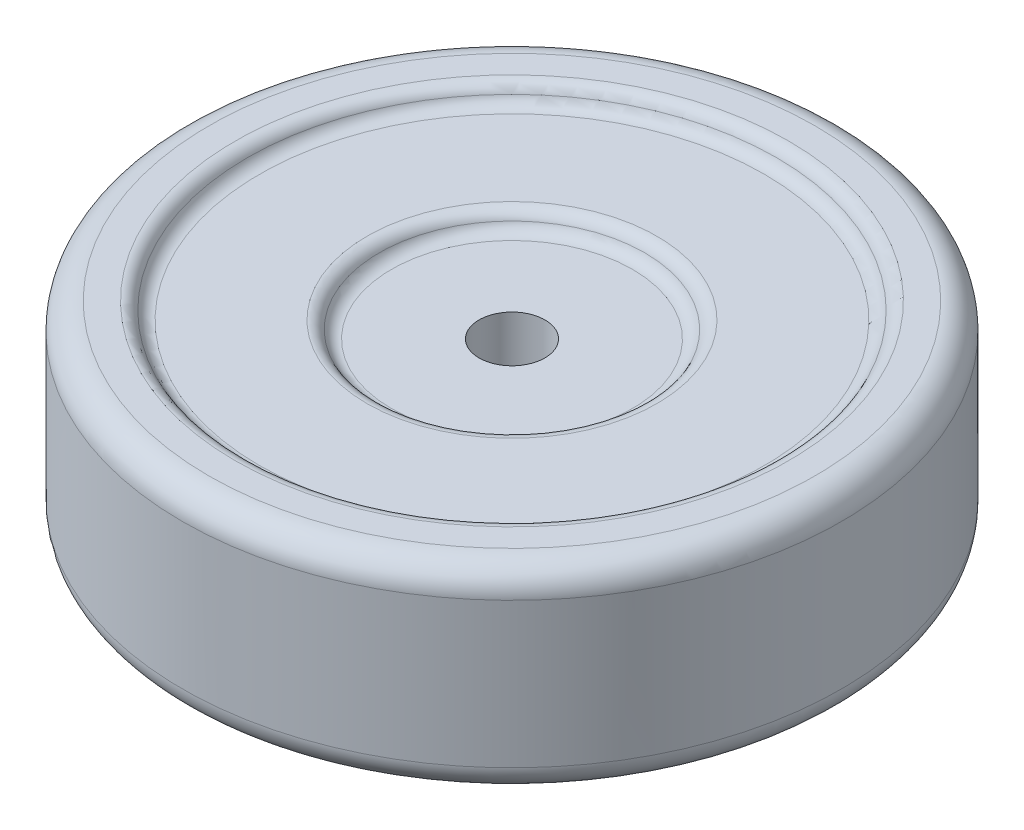
SolidWorks part; units mm, degrees
material "Hexcel AS4C (3000 Filaments)"
ref_plane "Front Plane" through (0, 0, 0) normal (0, 0, 1) x (1, 0, 0)
ref_plane "Top Plane" through (0, 0, 0) normal (0, 1, 0) x (1, 0, 0)
ref_plane "Right Plane" through (0, 0, 0) normal (1, 0, 0) x (0, 0, -1)
sketch "Sketch1" plane through (0, 0, 0) normal (0, 1, 0) x (1, 0, 0)
  circle A0 centre (0, 0) radius 127
extrude "Boss-Extrude1" add sketch "Sketch1" along normal blind 38.1
sketch "Sketch2" plane through (0, 38.1, 0) normal (0, 1, 0) x (1, 0, 0)
  circle A0 centre (0, 0) radius 101.6
extrude "Cut-Extrude1" cut sketch "Sketch2" against normal blind 6.35
sketch "Sketch3" plane through (0, 31.75, 0) normal (0, 1, 0) x (1, 0, 0)
  circle A0 centre (0, 0) radius 50.8
extrude "Cut-Extrude2" cut sketch "Sketch3" against normal blind 6.35
sketch "Sketch4" plane through (0, 25.4, 0) normal (0, 1, 0) x (1, 0, 0)
  circle A0 centre (0, 0) radius 12.7
  dimension "D1" = 25.4
extrude "Cut-Extrude3" cut sketch "Sketch4" against normal blind 77.978
fillet "Fillet1" radius 10.16 1 edges at (0, 38.1, 127)
fillet "Fillet2" radius 5.08 1 edges at (0, 38.1, 101.6)
fillet "Fillet3" radius 5.08 1 edges at (0, 31.75, 101.6)
fillet "Fillet4" radius 5.08 1 edges at (0, 31.75, 50.8)
fillet "Fillet5" radius 5.08 1 edges at (0, 25.4, 50.8)
mirror "Mirror1" about plane through (0, 0, 0) normal (0, 1, 0) of "Fillet5", "Fillet4", "Fillet3", "Fillet2", "Fillet1", "Cut-Extrude2", "Cut-Extrude3", "Cut-Extrude1", "Boss-Extrude1"
